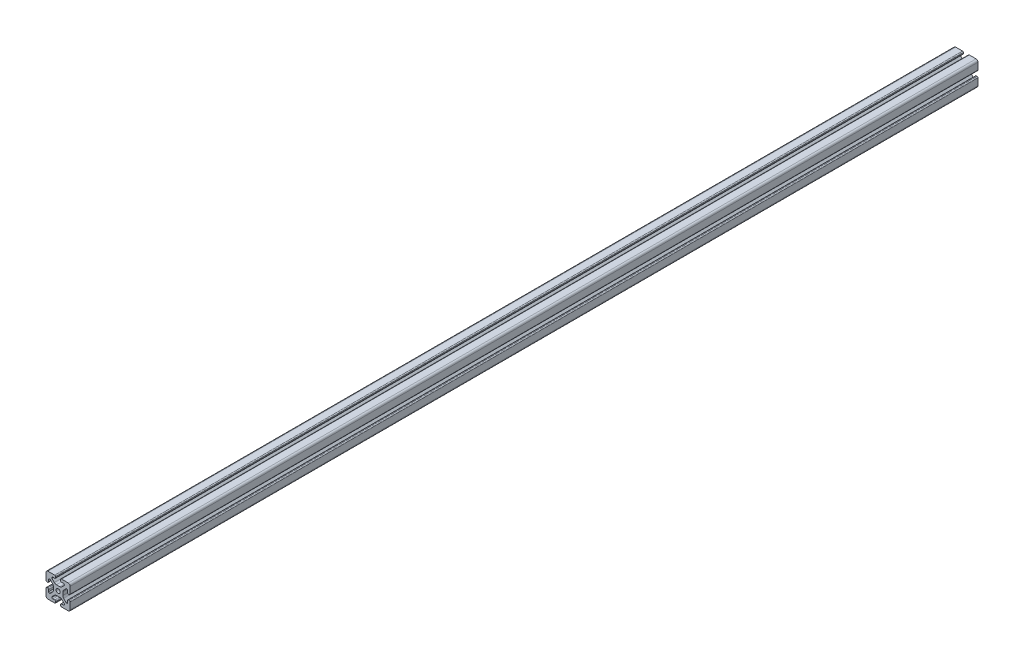
SolidWorks part; units mm, degrees
ref_plane "Front Plane" through (0, 0, 0) normal (0, 0, 1) x (1, 0, 0)
ref_plane "Top Plane" through (0, 0, 0) normal (0, 1, 0) x (1, 0, 0)
ref_plane "Right Plane" through (0, 0, 0) normal (1, 0, 0) x (0, 0, -1)
sketch "Sketch1" plane through (0, 0, 0) normal (0, 0, 1) x (1, 0, 0)
  line L0 (0, 19.7407) -> (0, -19.7407) construction
  line L1 (19.0335, 0) -> (-20.7246, 0) construction
  line L2 (-8.715, -15.5246) -> (-5.63, -15.5246)
  line L3 (-10.285, -13.9546) -> (-10.285, -13.4925)
  line L4 (-6.2171, -9.1098) -> (-10.0624, -12.9551)
  line L5 (2.7773, -7.685) -> (-2.7773, -7.685)
  line L6 (10.0624, -12.9551) -> (6.2171, -9.1098)
  line L7 (10.285, -13.9546) -> (10.285, -13.4925)
  line L8 (5.63, -15.5246) -> (8.715, -15.5246)
  line L9 (4.06, -18.43) -> (4.06, -17.0946)
  line L10 (-4.06, -18.43) -> (-4.06, -17.0946)
  line L11 (15.68, -8.7154) -> (15.68, -5.63)
  line L12 (-14.11, -10.2854) -> (-13.8169, -10.2854)
  line L13 (20, -16.83) -> (20, -5.63)
  line L14 (20, 5.63) -> (20, 13.0011)
  line L15 (-16.83, 20) -> (-5.63, 20)
  line L16 (5.63, 20) -> (12.9796, 20)
  line L17 (-8.715, 15.5246) -> (-5.63, 15.5246)
  line L18 (-20, -17.0184) -> (-20, -5.7579)
  line L19 (-20, 5.573) -> (-20, 13.0045)
  line L20 (-15.68, -8.7154) -> (-15.68, -5.7579)
  line L21 (-16.6746, -20) -> (-5.63, -20)
  line L22 (5.63, -20) -> (13, -20)
  line L23 (14.11, -10.2854) -> (13.6201, -10.2854)
  line L24 (13.1637, -9.947) -> (9.0762, -5.8595)
  line L25 (7.685, -2.5008) -> (7.685, 2.5008)
  line L26 (9.0762, 5.8595) -> (13.2795, 10.0628)
  line L27 (13.8169, 10.2854) -> (14.11, 10.2854)
  line L28 (15.68, 8.7154) -> (15.68, 5.63)
  line L29 (17.25, 4.06) -> (18.43, 4.06)
  line L30 (20, 13.0011) -> (20, 16.83)
  line L31 (16.83, 20) -> (12.9796, 20)
  line L32 (4.06, 18.43) -> (4.06, 17.0946)
  line L33 (5.63, 15.5246) -> (8.715, 15.5246)
  line L34 (10.285, 13.9546) -> (10.285, 13.4925)
  line L35 (10.0624, 12.9551) -> (6.2171, 9.1098)
  line L36 (2.7773, 7.685) -> (-2.7773, 7.685)
  line L37 (-6.2171, 9.1098) -> (-10.0624, 12.9551)
  line L38 (-10.285, 13.4925) -> (-10.285, 13.9546)
  line L39 (-4.06, 17.0946) -> (-4.06, 18.43)
  line L40 (-20, 16.83) -> (-20, 13.0045)
  line L41 (-18.43, 4.003) -> (-17.25, 4.003)
  line L42 (-15.68, 5.573) -> (-15.68, 8.4757)
  line L43 (-14.0552, 10.0447) -> (-13.7199, 10.033)
  line L44 (-13.0405, 9.8238) -> (-9.0762, 5.8595)
  line L45 (-7.685, 2.5008) -> (-7.685, -2.5008)
  line L46 (-9.0762, -5.8595) -> (-13.2795, -10.0628)
  line L47 (-17.2485, -4.1204) -> (-18.43, -4.1204)
  line L48 (13, -20) -> (16.83, -20)
  line L49 (18.43, -4.06) -> (17.25, -4.06)
  arc A0 (-5.63, -15.5246) -> (-4.06, -17.0946) centre (-5.63, -17.0946) cw
  arc A1 (-8.715, -15.5246) -> (-10.285, -13.9546) centre (-8.715, -13.9546) cw
  arc A2 (-10.285, -13.4925) -> (-10.0624, -12.9551) centre (-9.525, -13.4925) cw
  arc A3 (-6.2171, -9.1098) -> (-2.7773, -7.685) centre (-2.7773, -12.5496) cw
  arc A4 (2.7773, -7.685) -> (6.2171, -9.1098) centre (2.7773, -12.5496) cw
  arc A5 (10.0624, -12.9551) -> (10.285, -13.4925) centre (9.525, -13.4925) cw
  arc A6 (10.285, -13.9546) -> (8.715, -15.5246) centre (8.715, -13.9546) cw
  arc A7 (4.06, -17.0946) -> (5.63, -15.5246) centre (5.63, -17.0946) cw
  arc A8 (5.63, -20) -> (4.06, -18.43) centre (5.63, -18.43) cw
  arc A9 (-4.06, -18.43) -> (-5.63, -20) centre (-5.63, -18.43) cw
  circle A10 centre (0, 0) radius 3.4
  arc A11 (17.25, -4.06) -> (15.68, -5.63) centre (17.25, -5.63) ccw
  arc A12 (14.11, -10.2854) -> (15.68, -8.7154) centre (14.11, -8.7154) ccw
  arc A13 (13.1637, -9.947) -> (13.6201, -10.2854) centre (13.8117, -9.55) ccw
  arc A14 (7.685, -2.5008) -> (9.0762, -5.8595) centre (12.435, -2.5008) ccw
  arc A15 (9.0762, 5.8595) -> (7.685, 2.5008) centre (12.435, 2.5008) ccw
  arc A16 (13.8169, 10.2854) -> (13.2795, 10.0628) centre (13.8169, 9.5254) ccw
  arc A17 (15.68, 8.7154) -> (14.11, 10.2854) centre (14.11, 8.7154) ccw
  arc A18 (15.68, 5.63) -> (17.25, 4.06) centre (17.25, 5.63) ccw
  arc A19 (18.43, 4.06) -> (20, 5.63) centre (18.43, 5.63) ccw
  arc A20 (20, 16.83) -> (16.83, 20) centre (16.83, 16.83) ccw
  arc A21 (5.63, 20) -> (4.06, 18.43) centre (5.63, 18.43) ccw
  arc A22 (4.06, 17.0946) -> (5.63, 15.5246) centre (5.63, 17.0946) ccw
  arc A23 (10.285, 13.9546) -> (8.715, 15.5246) centre (8.715, 13.9546) ccw
  arc A24 (10.0624, 12.9551) -> (10.285, 13.4925) centre (9.525, 13.4925) ccw
  arc A25 (2.7773, 7.685) -> (6.2171, 9.1098) centre (2.7773, 12.5496) ccw
  arc A26 (-6.2171, 9.1098) -> (-2.7773, 7.685) centre (-2.7773, 12.5496) ccw
  arc A27 (-10.285, 13.4925) -> (-10.0624, 12.9551) centre (-9.525, 13.4925) ccw
  arc A28 (-8.715, 15.5246) -> (-10.285, 13.9546) centre (-8.715, 13.9546) ccw
  arc A29 (-5.63, 15.5246) -> (-4.06, 17.0946) centre (-5.63, 17.0946) ccw
  arc A30 (-4.06, 18.43) -> (-5.63, 20) centre (-5.63, 18.43) ccw
  arc A31 (-16.83, 20) -> (-20, 16.83) centre (-16.83, 16.83) ccw
  arc A32 (-20, 5.573) -> (-18.43, 4.003) centre (-18.43, 5.573) ccw
  arc A33 (-17.25, 4.003) -> (-15.68, 5.573) centre (-17.25, 5.573) ccw
  arc A34 (-14.0552, 10.0447) -> (-15.68, 8.4757) centre (-14.11, 8.4757) ccw
  arc A35 (-13.0405, 9.8238) -> (-13.7199, 10.033) centre (-13.5779, 9.2864) ccw
  arc A36 (-7.685, 2.5008) -> (-9.0762, 5.8595) centre (-12.435, 2.5008) ccw
  arc A37 (-9.0762, -5.8595) -> (-7.685, -2.5008) centre (-12.435, -2.5008) ccw
  arc A38 (-13.8169, -10.2854) -> (-13.2795, -10.0628) centre (-13.8169, -9.5254) ccw
  arc A39 (-15.68, -8.7154) -> (-14.11, -10.2854) centre (-14.11, -8.7154) ccw
  arc A40 (-15.68, -5.7579) -> (-17.2485, -4.1204) centre (-17.2485, -5.6904) ccw
  arc A41 (-18.43, -4.1204) -> (-20, -5.7579) centre (-18.4315, -5.6904) ccw
  arc A42 (-20, -17.0184) -> (-16.6746, -20) centre (-16.8354, -16.8341) ccw
  arc A43 (16.83, -20) -> (20, -16.83) centre (16.83, -16.83) ccw
  arc A44 (20, -5.63) -> (18.43, -4.06) centre (18.43, -5.63) ccw
  dimension "D1" = 6.8
  dimension "D2" = 4.32
  dimension "D3" = 15.37
  dimension "D4" = 20.57
  dimension "D5" = 15.37
  dimension "D6" = 40
  dimension "D7" = 20
  dimension "D8" = 4.32
  dimension "D9" = 8.12
extrude "Boss-Extrude1" add sketch "Sketch1" along normal blind 1500
